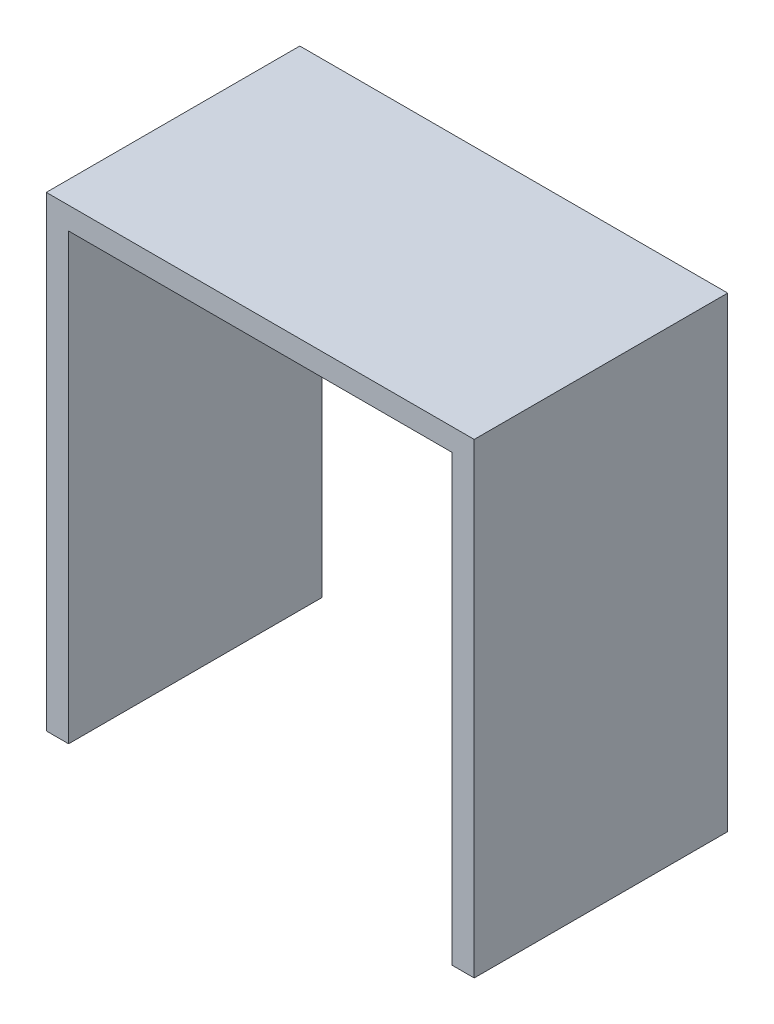
SolidWorks part; units mm, degrees
ref_plane "Front Plane" through (0, 0, 0) normal (0, 0, 1) x (1, 0, 0)
ref_plane "Top Plane" through (0, 0, 0) normal (0, 1, 0) x (1, 0, 0)
ref_plane "Right Plane" through (0, 0, 0) normal (1, 0, 0) x (0, 0, -1)
sketch "Sketch1" plane through (0, 0, 0) normal (0, 0, 1) x (1, 0, 0)
  line L0 (0, 0) -> (0, 46)
  line L1 (0, 46) -> (42.2, 46)
  line L2 (42.2, 46) -> (42.2, 0)
  line L3 (42.2, 0) -> (40, 0)
  line L4 (40, 0) -> (40, 43.8)
  line L5 (40, 43.8) -> (2.2, 43.8)
  line L6 (2.2, 43.8) -> (2.2, 0)
  line L7 (2.2, 0) -> (0, 0)
  dimension "D1" = 46
  dimension "D2" = 42.2
  dimension "D3" = 2.2
  dimension "D4" = 2.2
  dimension "D5" = 2.2
extrude "Boss-Extrude1" add sketch "Sketch1" along normal blind 25
